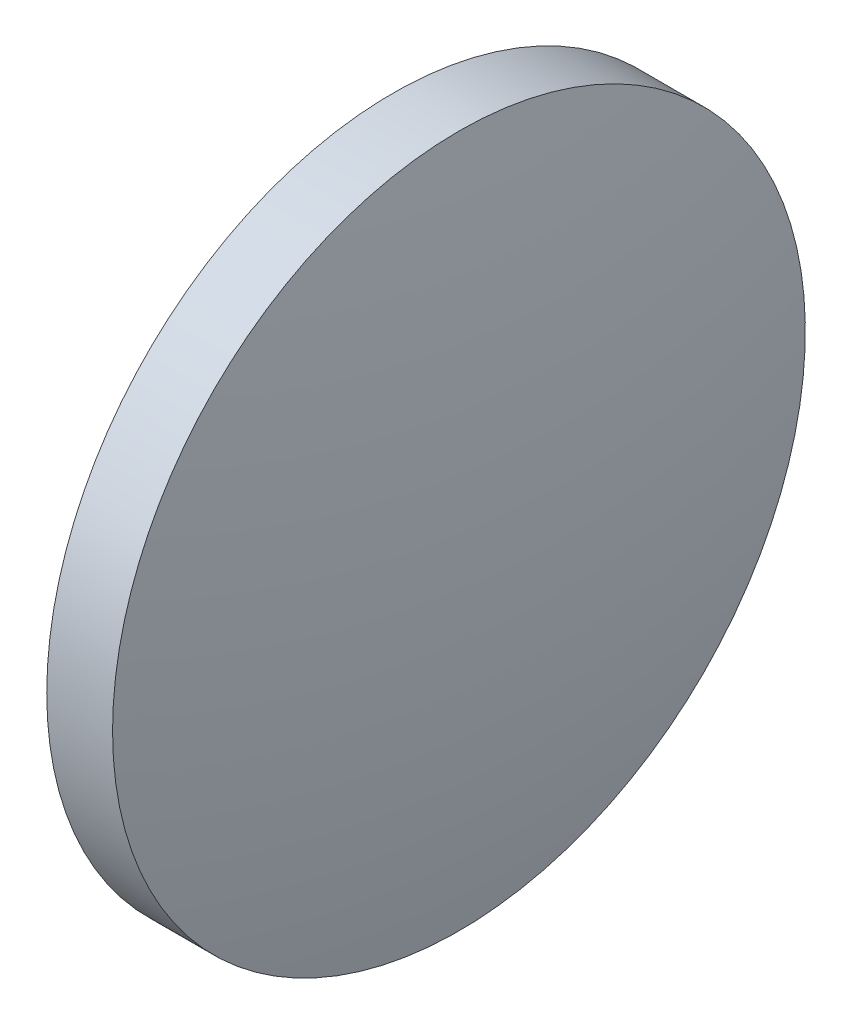
SolidWorks part; units mm, degrees
ref_plane "前视基准面" through (0, 0, 0) normal (0, 0, 1) x (1, 0, 0)
ref_plane "上视基准面" through (0, 0, 0) normal (0, 1, 0) x (1, 0, 0)
ref_plane "右视基准面" through (0, 0, 0) normal (1, 0, 0) x (0, 0, -1)
sketch "草图2" plane through (0, 0, 0) normal (0, 0, 1) x (1, 0, 0)
  line L0 (404.4422, 111.0798) -> (415.1988, 111.0798) construction
  line L1 (408.1675, 111.0798) -> (408.1675, 119.0798)
  line L2 (408.1675, 119.0798) -> (409.6875, 119.0798)
  line L3 (408.1675, 111.0798) -> (410.4675, 111.0798)
  arc A0 (410.4675, 111.0798) -> (409.6875, 119.0798) centre (369.0519, 111.0798) ccw
revolve "旋转1" add sketch "草图2" angle 360 about L0
